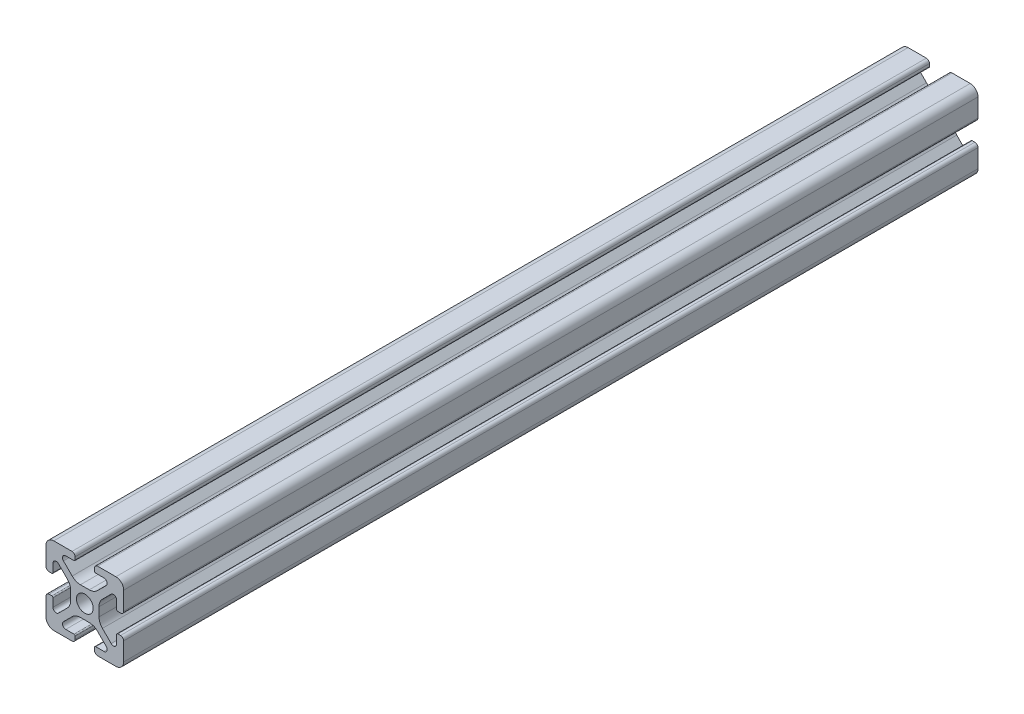
SolidWorks part; units mm, degrees
ref_plane "Front" through (0, 0, 0) normal (0, 0, 1) x (1, 0, 0)
ref_plane "Top" through (0, 0, 0) normal (0, 1, 0) x (1, 0, 0)
ref_plane "Right" through (0, 0, 0) normal (1, 0, 0) x (0, 0, -1)
sketch "Support-Front" plane through (0, 0, 0) normal (0, 0, 1) x (1, 0, 0)
  line L0 (10, 0) -> (-10, 0) construction
  line L1 (-10, -10) -> (10, -10)
  line L2 (-10, -10) -> (-10, 10)
  line L3 (-10, 10) -> (10, 10)
  line L4 (10, -10) -> (10, 10)
  line L5 (0, 10) -> (0, -10) construction
  dimension "Height-Profile" = 20
  dimension "Width-Profile" = 20
sketch "Support-Right-Length" plane through (0, 0, 0) normal (1, 0, 0) x (0, 0, -1)
  line L0 (0, -10) -> (0, 10) construction
  line L1 (-25, 10) -> (25, 10)
  line L2 (-25, 10) -> (-25, -10)
  line L3 (-25, -10) -> (25, -10)
  line L4 (25, 10) -> (25, -10)
  dimension "Length-Profile" = 50
sketch "Support-Profile" plane through (0, 0, 0) normal (0, 0, 1) x (1, 0, 0)
  line L8 (4.9176, -8.2) -> (2.8, -8.2)
  line L9 (2.5, -8.5) -> (2.5, -9.2)
  line L10 (3.3, -10) -> (8, -10)
  line L11 (10, -8) -> (10, -3.3)
  line L24 (9.2, -2.5) -> (8.5, -2.5)
  line L25 (8.2, -2.8) -> (8.2, -4.9176)
  line L26 (6.779, -5.5062) -> (4.5287, -3.2559)
  line L27 (3.65, -1.1346) -> (3.65, 1.1346)
  line L28 (4.5287, 3.2559) -> (6.779, 5.5062)
  line L29 (8.2, 4.9176) -> (8.2, 2.8)
  line L30 (8.5, 2.5) -> (9.2, 2.5)
  line L31 (10, 3.3) -> (10, 8)
  line L32 (8, 10) -> (3.3, 10)
  line L33 (2.5, 9.2) -> (2.5, 8.5)
  line L34 (2.8, 8.2) -> (4.9176, 8.2)
  line L35 (5.5062, 6.779) -> (3.2559, 4.5287)
  line L40 (1.1346, 3.65) -> (-1.1346, 3.65)
  line L41 (-3.2559, 4.5287) -> (-5.5062, 6.779)
  line L42 (-4.9176, 8.2) -> (-2.8, 8.2)
  line L43 (-2.5, 8.5) -> (-2.5, 9.2)
  line L44 (-3.3, 10) -> (-8, 10)
  line L45 (-10, 8) -> (-10, 3.3)
  line L46 (-9.2, 2.5) -> (-8.5, 2.5)
  line L47 (-8.2, 2.8) -> (-8.2, 4.9176)
  line L48 (-6.779, 5.5062) -> (-4.5287, 3.2559)
  line L49 (-3.65, 1.1346) -> (-3.65, -1.1346)
  line L50 (-4.5287, -3.2559) -> (-6.779, -5.5062)
  line L51 (-8.2, -4.9176) -> (-8.2, -2.8)
  line L52 (-8.5, -2.5) -> (-9.2, -2.5)
  line L53 (-10, -3.3) -> (-10, -8)
  line L54 (-8, -10) -> (-3.3, -10)
  line L55 (-2.5, -9.2) -> (-2.5, -8.5)
  line L56 (-2.8, -8.2) -> (-4.9176, -8.2)
  line L57 (-5.5062, -6.779) -> (-3.2559, -4.5287)
  line L58 (-1.1346, -3.65) -> (1.1346, -3.65)
  line L59 (3.2559, -4.5287) -> (5.5062, -6.779)
  circle A2 centre (0, 0) radius 2.15
  arc A3 (2.8, -8.2) -> (2.5, -8.5) centre (2.8, -8.5) ccw
  arc A5 (2.5, -9.2) -> (3.3, -10) centre (3.3, -9.2) ccw
  arc A24 (8, -10) -> (10, -8) centre (8, -8) ccw
  arc A25 (10, -3.3) -> (9.2, -2.5) centre (9.2, -3.3) ccw
  arc A26 (8.5, -2.5) -> (8.2, -2.8) centre (8.5, -2.8) ccw
  arc A27 (6.779, -5.5062) -> (8.2, -4.9176) centre (7.3676, -4.9176) ccw
  arc A28 (3.65, -1.1346) -> (4.5287, -3.2559) centre (6.65, -1.1346) ccw
  arc A29 (4.5287, 3.2559) -> (3.65, 1.1346) centre (6.65, 1.1346) ccw
  arc A30 (8.2, 4.9176) -> (6.779, 5.5062) centre (7.3676, 4.9176) ccw
  arc A31 (8.2, 2.8) -> (8.5, 2.5) centre (8.5, 2.8) ccw
  arc A32 (9.2, 2.5) -> (10, 3.3) centre (9.2, 3.3) ccw
  arc A33 (10, 8) -> (8, 10) centre (8, 8) ccw
  arc A34 (3.3, 10) -> (2.5, 9.2) centre (3.3, 9.2) ccw
  arc A35 (2.5, 8.5) -> (2.8, 8.2) centre (2.8, 8.5) ccw
  arc A38 (5.5062, 6.779) -> (4.9176, 8.2) centre (4.9176, 7.3676) ccw
  arc A39 (1.1346, 3.65) -> (3.2559, 4.5287) centre (1.1346, 6.65) ccw
  arc A44 (-3.2559, 4.5287) -> (-1.1346, 3.65) centre (-1.1346, 6.65) ccw
  arc A45 (-4.9176, 8.2) -> (-5.5062, 6.779) centre (-4.9176, 7.3676) ccw
  arc A46 (-2.8, 8.2) -> (-2.5, 8.5) centre (-2.8, 8.5) ccw
  arc A47 (-2.5, 9.2) -> (-3.3, 10) centre (-3.3, 9.2) ccw
  arc A48 (-8, 10) -> (-10, 8) centre (-8, 8) ccw
  arc A49 (-10, 3.3) -> (-9.2, 2.5) centre (-9.2, 3.3) ccw
  arc A50 (-8.5, 2.5) -> (-8.2, 2.8) centre (-8.5, 2.8) ccw
  arc A51 (-6.779, 5.5062) -> (-8.2, 4.9176) centre (-7.3676, 4.9176) ccw
  arc A52 (-3.65, 1.1346) -> (-4.5287, 3.2559) centre (-6.65, 1.1346) ccw
  arc A53 (-4.5287, -3.2559) -> (-3.65, -1.1346) centre (-6.65, -1.1346) ccw
  arc A54 (-8.2, -4.9176) -> (-6.779, -5.5062) centre (-7.3676, -4.9176) ccw
  arc A55 (-8.2, -2.8) -> (-8.5, -2.5) centre (-8.5, -2.8) ccw
  arc A56 (-9.2, -2.5) -> (-10, -3.3) centre (-9.2, -3.3) ccw
  arc A57 (-10, -8) -> (-8, -10) centre (-8, -8) ccw
  arc A58 (-3.3, -10) -> (-2.5, -9.2) centre (-3.3, -9.2) ccw
  arc A59 (-2.5, -8.5) -> (-2.8, -8.2) centre (-2.8, -8.5) ccw
  arc A60 (-5.5062, -6.779) -> (-4.9176, -8.2) centre (-4.9176, -7.3676) ccw
  arc A61 (-1.1346, -3.65) -> (-3.2559, -4.5287) centre (-1.1346, -6.65) ccw
  arc A62 (3.2559, -4.5287) -> (1.1346, -3.65) centre (1.1346, -6.65) ccw
  arc A63 (4.9176, -8.2) -> (5.5062, -6.779) centre (4.9176, -7.3676) ccw
ref_plane "Ref-Plane-1" through (0, 0, 25) normal (0, 0, 1) x (1, 0, 0)
ref_plane "Ref-Plane-2" through (0, 0, -25) normal (0, 0, 1) x (1, 0, 0)
sketch "Sketch4" plane through (0, 0, 25) normal (0, 0, 1) x (1, 0, 0)
  line L0 (-10, -10) -> (-10, 10) construction
  line L1 (-10, -10) -> (10, -10) construction
  line L2 (10, -10) -> (10, 10) construction
  line L3 (-10, 10) -> (10, 10) construction
  line L4 (-10, -10) -> (-10, 10)
  line L5 (-10, -10) -> (10, -10)
  line L6 (10, -10) -> (10, 10)
  line L7 (-10, 10) -> (10, 10)
extrude "Body" add sketch "Sketch4" against normal blind 220
sketch "Sketch16" plane through (0, 0, 0) normal (0, 0, 1) x (1, 0, 0)
  line L40 (4.9176, -8.2) -> (2.8, -8.2)
  line L41 (2.5, -8.5) -> (2.5, -9.2)
  line L42 (3.3, -10) -> (8, -10)
  line L43 (10, -8) -> (10, -3.3)
  line L44 (9.2, -2.5) -> (8.5, -2.5)
  line L45 (8.2, -2.8) -> (8.2, -4.9176)
  line L46 (6.779, -5.5062) -> (4.5287, -3.2559)
  line L47 (3.65, -1.1346) -> (3.65, 1.1346)
  line L48 (4.5287, 3.2559) -> (6.779, 5.5062)
  line L49 (8.2, 4.9176) -> (8.2, 2.8)
  line L50 (8.5, 2.5) -> (9.2, 2.5)
  line L51 (10, 3.3) -> (10, 8)
  line L52 (8, 10) -> (3.3, 10)
  line L53 (2.5, 9.2) -> (2.5, 8.5)
  line L54 (2.8, 8.2) -> (4.9176, 8.2)
  line L55 (5.5062, 6.779) -> (3.2559, 4.5287)
  line L56 (1.1346, 3.65) -> (-1.1346, 3.65)
  line L57 (-3.2559, 4.5287) -> (-5.5062, 6.779)
  line L58 (-4.9176, 8.2) -> (-2.8, 8.2)
  line L59 (-2.5, 8.5) -> (-2.5, 9.2)
  line L60 (-3.3, 10) -> (-8, 10)
  line L61 (-10, 8) -> (-10, 3.3)
  line L62 (-9.2, 2.5) -> (-8.5, 2.5)
  line L63 (-8.2, 2.8) -> (-8.2, 4.9176)
  line L64 (-6.779, 5.5062) -> (-4.5287, 3.2559)
  line L65 (-3.65, 1.1346) -> (-3.65, -1.1346)
  line L66 (-4.5287, -3.2559) -> (-6.779, -5.5062)
  line L67 (-8.2, -4.9176) -> (-8.2, -2.8)
  line L68 (-8.5, -2.5) -> (-9.2, -2.5)
  line L69 (-10, -3.3) -> (-10, -8)
  line L70 (-8, -10) -> (-3.3, -10)
  line L71 (-2.5, -9.2) -> (-2.5, -8.5)
  line L72 (-2.8, -8.2) -> (-4.9176, -8.2)
  line L73 (-5.5062, -6.779) -> (-3.2559, -4.5287)
  line L74 (-1.1346, -3.65) -> (1.1346, -3.65)
  line L75 (3.2559, -4.5287) -> (5.5062, -6.779)
  line L76 (4.9176, -8.2) -> (2.8, -8.2)
  line L77 (2.5, -8.5) -> (2.5, -9.2)
  line L78 (3.3, -10) -> (8, -10)
  line L79 (10, -8) -> (10, -3.3)
  line L80 (9.2, -2.5) -> (8.5, -2.5)
  line L81 (8.2, -2.8) -> (8.2, -4.9176)
  line L82 (6.779, -5.5062) -> (4.5287, -3.2559)
  line L83 (3.65, -1.1346) -> (3.65, 1.1346)
  line L84 (4.5287, 3.2559) -> (6.779, 5.5062)
  line L85 (8.2, 4.9176) -> (8.2, 2.8)
  line L86 (8.5, 2.5) -> (9.2, 2.5)
  line L87 (10, 3.3) -> (10, 8)
  line L88 (8, 10) -> (3.3, 10)
  line L89 (2.5, 9.2) -> (2.5, 8.5)
  line L90 (2.8, 8.2) -> (4.9176, 8.2)
  line L91 (5.5062, 6.779) -> (3.2559, 4.5287)
  line L92 (1.1346, 3.65) -> (-1.1346, 3.65)
  line L93 (-3.2559, 4.5287) -> (-5.5062, 6.779)
  line L94 (-4.9176, 8.2) -> (-2.8, 8.2)
  line L95 (-2.5, 8.5) -> (-2.5, 9.2)
  line L96 (-3.3, 10) -> (-8, 10)
  line L97 (-10, 8) -> (-10, 3.3)
  line L98 (-9.2, 2.5) -> (-8.5, 2.5)
  line L99 (-8.2, 2.8) -> (-8.2, 4.9176)
  line L100 (-6.779, 5.5062) -> (-4.5287, 3.2559)
  line L101 (-3.65, 1.1346) -> (-3.65, -1.1346)
  line L102 (-4.5287, -3.2559) -> (-6.779, -5.5062)
  line L103 (-8.2, -4.9176) -> (-8.2, -2.8)
  line L104 (-8.5, -2.5) -> (-9.2, -2.5)
  line L105 (-10, -3.3) -> (-10, -8)
  line L106 (-8, -10) -> (-3.3, -10)
  line L107 (-2.5, -9.2) -> (-2.5, -8.5)
  line L108 (-2.8, -8.2) -> (-4.9176, -8.2)
  line L109 (-5.5062, -6.779) -> (-3.2559, -4.5287)
  line L110 (-1.1346, -3.65) -> (1.1346, -3.65)
  line L111 (3.2559, -4.5287) -> (5.5062, -6.779)
  circle A7 centre (0, 0) radius 2.15 construction
  circle A8 centre (0, 0) radius 2.15
  arc A43 (2.8, -8.2) -> (2.5, -8.5) centre (2.8, -8.5) ccw
  arc A44 (2.5, -9.2) -> (3.3, -10) centre (3.3, -9.2) ccw
  arc A45 (8, -10) -> (10, -8) centre (8, -8) ccw
  arc A46 (10, -3.3) -> (9.2, -2.5) centre (9.2, -3.3) ccw
  arc A47 (8.5, -2.5) -> (8.2, -2.8) centre (8.5, -2.8) ccw
  arc A48 (6.779, -5.5062) -> (8.2, -4.9176) centre (7.3676, -4.9176) ccw
  arc A49 (3.65, -1.1346) -> (4.5287, -3.2559) centre (6.65, -1.1346) ccw
  arc A50 (4.5287, 3.2559) -> (3.65, 1.1346) centre (6.65, 1.1346) ccw
  arc A51 (8.2, 4.9176) -> (6.779, 5.5062) centre (7.3676, 4.9176) ccw
  arc A52 (8.2, 2.8) -> (8.5, 2.5) centre (8.5, 2.8) ccw
  arc A53 (9.2, 2.5) -> (10, 3.3) centre (9.2, 3.3) ccw
  arc A54 (10, 8) -> (8, 10) centre (8, 8) ccw
  arc A55 (3.3, 10) -> (2.5, 9.2) centre (3.3, 9.2) ccw
  arc A56 (2.5, 8.5) -> (2.8, 8.2) centre (2.8, 8.5) ccw
  arc A57 (5.5062, 6.779) -> (4.9176, 8.2) centre (4.9176, 7.3676) ccw
  arc A58 (1.1346, 3.65) -> (3.2559, 4.5287) centre (1.1346, 6.65) ccw
  arc A59 (-3.2559, 4.5287) -> (-1.1346, 3.65) centre (-1.1346, 6.65) ccw
  arc A60 (-4.9176, 8.2) -> (-5.5062, 6.779) centre (-4.9176, 7.3676) ccw
  arc A61 (-2.8, 8.2) -> (-2.5, 8.5) centre (-2.8, 8.5) ccw
  arc A62 (-2.5, 9.2) -> (-3.3, 10) centre (-3.3, 9.2) ccw
  arc A63 (-8, 10) -> (-10, 8) centre (-8, 8) ccw
  arc A64 (-10, 3.3) -> (-9.2, 2.5) centre (-9.2, 3.3) ccw
  arc A65 (-8.5, 2.5) -> (-8.2, 2.8) centre (-8.5, 2.8) ccw
  arc A66 (-6.779, 5.5062) -> (-8.2, 4.9176) centre (-7.3676, 4.9176) ccw
  arc A67 (-3.65, 1.1346) -> (-4.5287, 3.2559) centre (-6.65, 1.1346) ccw
  arc A68 (-4.5287, -3.2559) -> (-3.65, -1.1346) centre (-6.65, -1.1346) ccw
  arc A69 (-8.2, -4.9176) -> (-6.779, -5.5062) centre (-7.3676, -4.9176) ccw
  arc A70 (-8.2, -2.8) -> (-8.5, -2.5) centre (-8.5, -2.8) ccw
  arc A71 (-9.2, -2.5) -> (-10, -3.3) centre (-9.2, -3.3) ccw
  arc A72 (-10, -8) -> (-8, -10) centre (-8, -8) ccw
  arc A73 (-3.3, -10) -> (-2.5, -9.2) centre (-3.3, -9.2) ccw
  arc A74 (-2.5, -8.5) -> (-2.8, -8.2) centre (-2.8, -8.5) ccw
  arc A75 (-5.5062, -6.779) -> (-4.9176, -8.2) centre (-4.9176, -7.3676) ccw
  arc A76 (-1.1346, -3.65) -> (-3.2559, -4.5287) centre (-1.1346, -6.65) ccw
  arc A77 (3.2559, -4.5287) -> (1.1346, -3.65) centre (1.1346, -6.65) ccw
  arc A78 (4.9176, -8.2) -> (5.5062, -6.779) centre (4.9176, -7.3676) ccw
  arc A79 (2.8, -8.2) -> (2.5, -8.5) centre (2.8, -8.5) ccw
  arc A80 (2.5, -9.2) -> (3.3, -10) centre (3.3, -9.2) ccw
  arc A81 (8, -10) -> (10, -8) centre (8, -8) ccw
  arc A82 (10, -3.3) -> (9.2, -2.5) centre (9.2, -3.3) ccw
  arc A83 (8.5, -2.5) -> (8.2, -2.8) centre (8.5, -2.8) ccw
  arc A84 (6.779, -5.5062) -> (8.2, -4.9176) centre (7.3676, -4.9176) ccw
  arc A85 (3.65, -1.1346) -> (4.5287, -3.2559) centre (6.65, -1.1346) ccw
  arc A86 (4.5287, 3.2559) -> (3.65, 1.1346) centre (6.65, 1.1346) ccw
  arc A87 (8.2, 4.9176) -> (6.779, 5.5062) centre (7.3676, 4.9176) ccw
  arc A88 (8.2, 2.8) -> (8.5, 2.5) centre (8.5, 2.8) ccw
  arc A89 (9.2, 2.5) -> (10, 3.3) centre (9.2, 3.3) ccw
  arc A90 (10, 8) -> (8, 10) centre (8, 8) ccw
  arc A91 (3.3, 10) -> (2.5, 9.2) centre (3.3, 9.2) ccw
  arc A92 (2.5, 8.5) -> (2.8, 8.2) centre (2.8, 8.5) ccw
  arc A93 (5.5062, 6.779) -> (4.9176, 8.2) centre (4.9176, 7.3676) ccw
  arc A94 (1.1346, 3.65) -> (3.2559, 4.5287) centre (1.1346, 6.65) ccw
  arc A95 (-3.2559, 4.5287) -> (-1.1346, 3.65) centre (-1.1346, 6.65) ccw
  arc A96 (-4.9176, 8.2) -> (-5.5062, 6.779) centre (-4.9176, 7.3676) ccw
  arc A97 (-2.8, 8.2) -> (-2.5, 8.5) centre (-2.8, 8.5) ccw
  arc A98 (-2.5, 9.2) -> (-3.3, 10) centre (-3.3, 9.2) ccw
  arc A99 (-8, 10) -> (-10, 8) centre (-8, 8) ccw
  arc A100 (-10, 3.3) -> (-9.2, 2.5) centre (-9.2, 3.3) ccw
  arc A101 (-8.5, 2.5) -> (-8.2, 2.8) centre (-8.5, 2.8) ccw
  arc A102 (-6.779, 5.5062) -> (-8.2, 4.9176) centre (-7.3676, 4.9176) ccw
  arc A103 (-3.65, 1.1346) -> (-4.5287, 3.2559) centre (-6.65, 1.1346) ccw
  arc A104 (-4.5287, -3.2559) -> (-3.65, -1.1346) centre (-6.65, -1.1346) ccw
  arc A105 (-8.2, -4.9176) -> (-6.779, -5.5062) centre (-7.3676, -4.9176) ccw
  arc A106 (-8.2, -2.8) -> (-8.5, -2.5) centre (-8.5, -2.8) ccw
  arc A107 (-9.2, -2.5) -> (-10, -3.3) centre (-9.2, -3.3) ccw
  arc A108 (-10, -8) -> (-8, -10) centre (-8, -8) ccw
  arc A109 (-3.3, -10) -> (-2.5, -9.2) centre (-3.3, -9.2) ccw
  arc A110 (-2.5, -8.5) -> (-2.8, -8.2) centre (-2.8, -8.5) ccw
  arc A111 (-5.5062, -6.779) -> (-4.9176, -8.2) centre (-4.9176, -7.3676) ccw
  arc A112 (-1.1346, -3.65) -> (-3.2559, -4.5287) centre (-1.1346, -6.65) ccw
  arc A113 (3.2559, -4.5287) -> (1.1346, -3.65) centre (1.1346, -6.65) ccw
  arc A114 (4.9176, -8.2) -> (5.5062, -6.779) centre (4.9176, -7.3676) ccw
  dimension "D1" = 0
extrude "Cut-Profile" cut sketch "Sketch16" against normal through all and the other way through all flip side to cut
